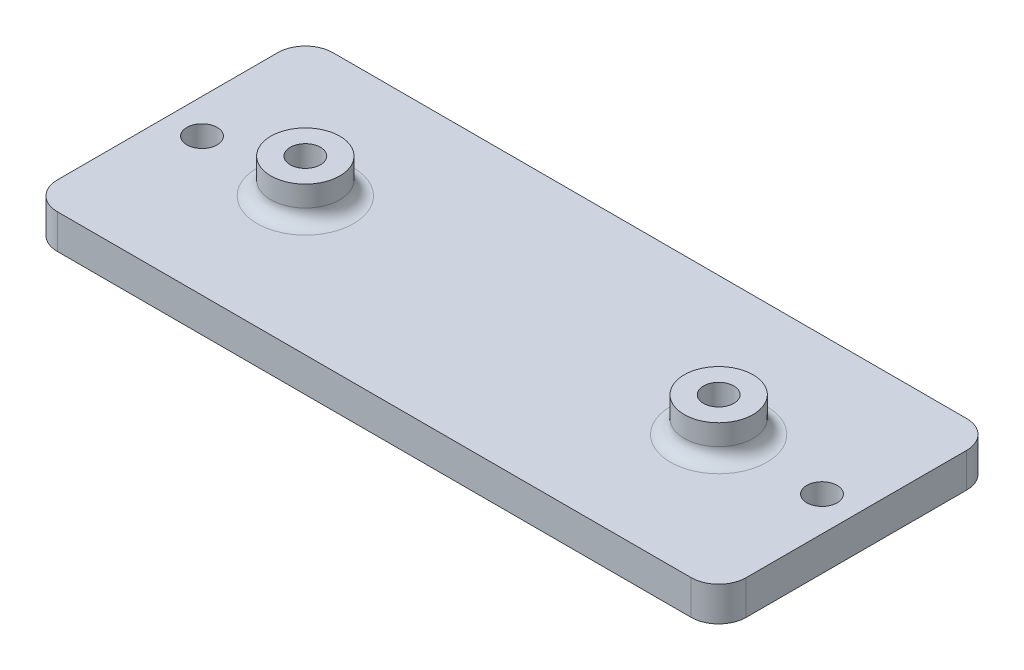
SolidWorks part; units mm, degrees
ref_plane "Front" through (0, 0, 0) normal (0, 0, 1) x (1, 0, 0)
ref_plane "Top" through (0, 0, 0) normal (0, 1, 0) x (1, 0, 0)
ref_plane "Right" through (0, 0, 0) normal (1, 0, 0) x (0, 0, -1)
sketch "Sketch1" plane through (0, 0, 0) normal (0, 1, 0) x (1, 0, 0)
  line L1 (-29.21, -12.7) -> (29.21, -12.7)
  line L2 (-31.75, -10.16) -> (-31.75, 10.16)
  line L3 (-29.21, 12.7) -> (29.21, 12.7)
  line L4 (31.75, -10.16) -> (31.75, 10.16)
  line L5 (-31.75, -12.7) -> (31.75, 12.7) construction
  line L6 (-31.75, 12.7) -> (31.75, -12.7) construction
  arc A0 (-29.21, -12.7) -> (-31.75, -10.16) centre (-29.21, -10.16) cw
  arc A1 (29.21, -12.7) -> (31.75, -10.16) centre (29.21, -10.16) ccw
  arc A2 (29.21, 12.7) -> (31.75, 10.16) centre (29.21, 10.16) cw
  arc A3 (-31.75, 10.16) -> (-29.21, 12.7) centre (-29.21, 10.16) cw
  point P0 (0, 0)
  dimension "D3" = 2.54
  dimension "D1" = 25.4
  dimension "D2" = 63.5
extrude "Boss-Extrude1" add sketch "Sketch1" along normal blind 3.175
sketch "Sketch2" plane through (0, 3.175, 0) normal (0, 1, 0) x (1, 0, 0)
  line L0 (0, 0) -> (-19.05, 0) construction
  line L1 (0, 0) -> (0, 12.7) construction
  line L2 (29.21, 12.7) -> (-29.21, 12.7) construction
  circle A0 centre (-19.05, 0) radius 3.175
  circle A1 centre (19.05, 0) radius 3.175
  dimension "D2" = 6.35
  dimension "D1" = 19.05
extrude "Boss-Extrude2" add sketch "Sketch2" along normal blind 3.175
sketch "Sketch3" plane through (0, 6.35, 0) normal (0, 1, 0) x (1, 0, 0)
  circle A0 centre (-19.05, 0) radius 1.397
  circle A1 centre (19.05, 0) radius 1.397
  dimension "D1" = 2.794
  dimension "D2" = 2.794
extrude "Cut-Extrude1" cut sketch "Sketch3" against normal through all
fillet "Fillet1" radius 1.27 2 edges at (19.05, 3.175, -3.175) (-19.05, 3.175, 3.175)
sketch "Sketch4" plane through (0, 3.175, 0) normal (0, 1, 0) x (1, 0, 0)
  line L0 (0, -12.7) -> (0, 12.7) construction
  line L1 (-29.21, -12.7) -> (29.21, -12.7) construction
  line L2 (29.21, 12.7) -> (-29.21, 12.7) construction
  line L3 (0, 0) -> (-25.4, 0) construction
  line L4 (-28.575, 0) -> (-31.75, 0) construction
  line L5 (-31.75, 10.16) -> (-31.75, -10.16) construction
  line L6 (-28.575, 0) -> (-25.4, 0) construction
  circle A0 centre (-28.575, 0) radius 1.397
  circle A1 centre (28.575, 0) radius 1.397
  dimension "D1" = 2.794
  dimension "D2" = 25.4
extrude "Cut-Extrude2" cut sketch "Sketch4" against normal up to next
